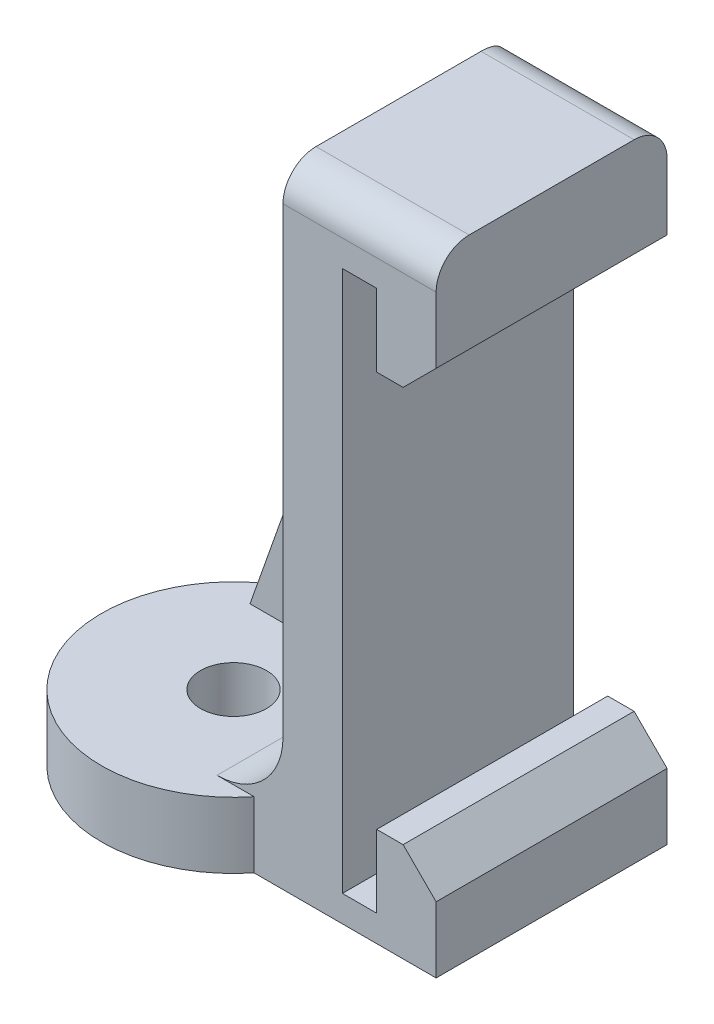
SolidWorks part; units mm, degrees
ref_plane "Front Plane" through (0, 0, 0) normal (0, 0, 1) x (1, 0, 0)
ref_plane "Top Plane" through (0, 0, 0) normal (0, 1, 0) x (1, 0, 0)
ref_plane "Right Plane" through (0, 0, 0) normal (1, 0, 0) x (0, 0, -1)
sketch "Sketch1" plane through (0, 0, 0) normal (0, 0, 1) x (1, 0, 0)
  line L0 (0, 0) -> (0, 25.4) construction
  line L1 (0, 25.4) -> (1.016, 25.4) construction
  line L2 (1.016, 25.4) -> (1.016, 0) construction
  line L3 (1.016, 0) -> (0, 0) construction
  line L4 (-0.3175, -0.3175) -> (-0.3175, 25.7175)
  line L5 (-0.3175, 25.7175) -> (1.3335, 25.7175)
  line L6 (1.3335, 25.7175) -> (1.3335, -0.3175) construction
  line L7 (1.3335, -0.3175) -> (-0.3175, -0.3175)
  line L8 (0.7937, 0) -> (0.7938, -1.5875) construction
  line L9 (1.016, 0) -> (4.191, 0) construction
  line L10 (4.191, -1.5875) -> (4.191, 0)
  line L11 (4.191, 0) -> (4.191, 3.175)
  line L12 (4.191, 3.175) -> (1.3335, 3.175)
  line L13 (1.016, 25.4) -> (1.016, 28.575) construction
  line L14 (1.016, 28.575) -> (4.191, 28.575)
  line L15 (4.191, 28.575) -> (4.191, 22.225)
  line L16 (4.191, 22.225) -> (1.3335, 22.225)
  line L17 (1.016, 28.575) -> (-3.175, 28.575)
  line L18 (-3.175, 28.575) -> (-3.175, -0.3175) construction
  line L20 (-3.175, -1.5875) -> (4.191, -1.5875)
  line L21 (-3.175, -1.5875) -> (-12.7, -1.5875)
  line L22 (-12.7, -1.5875) -> (-12.7, 1.5875)
  line L23 (-12.7, 1.5875) -> (-3.175, 1.5875)
  line L24 (1.3335, 25.7175) -> (1.3335, 22.225)
  line L25 (1.3335, 3.175) -> (1.3335, -0.3175)
  line L26 (-3.175, 28.575) -> (-3.175, 1.5875)
extrude "Boss-Extrude1" add sketch "Sketch1" along normal mid plane 19.05
fillet "Fillet1" radius 3.175 1 edges at (-3.175, 1.5875, 0)
sketch "Sketch2" plane through (0, 0, 0) normal (0, 0, 1) x (1, 0, 0)
  line L0 (-3.175, 28.575) -> (-12.7, 1.5875)
  line L1 (-12.7, 1.5875) -> (-3.175, 1.5875)
  line L2 (-3.175, 1.5875) -> (-3.175, 28.575)
extrude "Boss-Extrude2" add sketch "Sketch2" along normal mid plane 3.175
sketch "Sketch3" plane through (0, 1.5875, 0) normal (0, 1, 0) x (1, 0, 0)
  line L0 (-9.525, -9.525) -> (-9.525, -5.5563) construction
  line L1 (-6.35, -9.525) -> (-12.7, -9.525) construction
  line L2 (-9.525, 9.525) -> (-9.525, 5.5563) construction
  line L3 (-6.35, 9.525) -> (-12.7, 9.525) construction
  circle A0 centre (-9.525, -5.5563) radius 1.5875
  circle A1 centre (-9.525, 5.5563) radius 1.5875
extrude "Cut-Extrude1" cut sketch "Sketch3" against normal up to surface (3.175 mm away) up to face at (-4.2545, -1.5875, 0)
chamfer "Chamfer1" distance 1.5875 angle 45 2 edges at (4.191, 3.175, 0) (4.191, 22.225, 0)
fillet "Fillet2" radius 1.5875 2 edges at (0.508, 28.575, -9.525) (0.508, 28.575, 9.525)
sketch "Sketch4" plane through (0, 0, -1.5875) normal (0, 0, -1) x (-1, 0, 0)
  line L0 (12.7, 1.5875) -> (3.175, 28.575)
  line L1 (3.175, 28.575) -> (-4.191, 28.575)
  line L2 (-4.191, 28.575) -> (-4.191, -1.5875)
  line L3 (-4.191, -1.5875) -> (12.7, -1.5875)
  line L4 (12.7, -1.5875) -> (12.7, 1.5875)
extrude "Cut-Extrude2" cut sketch "Sketch4" along normal blind 12.7
fillet "Fillet3" radius 1.5875 1 edges at (0.508, 28.575, -1.5875)
sketch "Sketch5" plane through (0, 1.5875, 0) normal (0, 1, 0) x (1, 0, 0)
  circle A0 centre (-9.525, -5.5563) radius 6.35
  circle A1 centre (-9.525, -5.5563) radius 1.5875
extrude "Boss-Extrude3" add sketch "Sketch5" against normal blind 3.175
